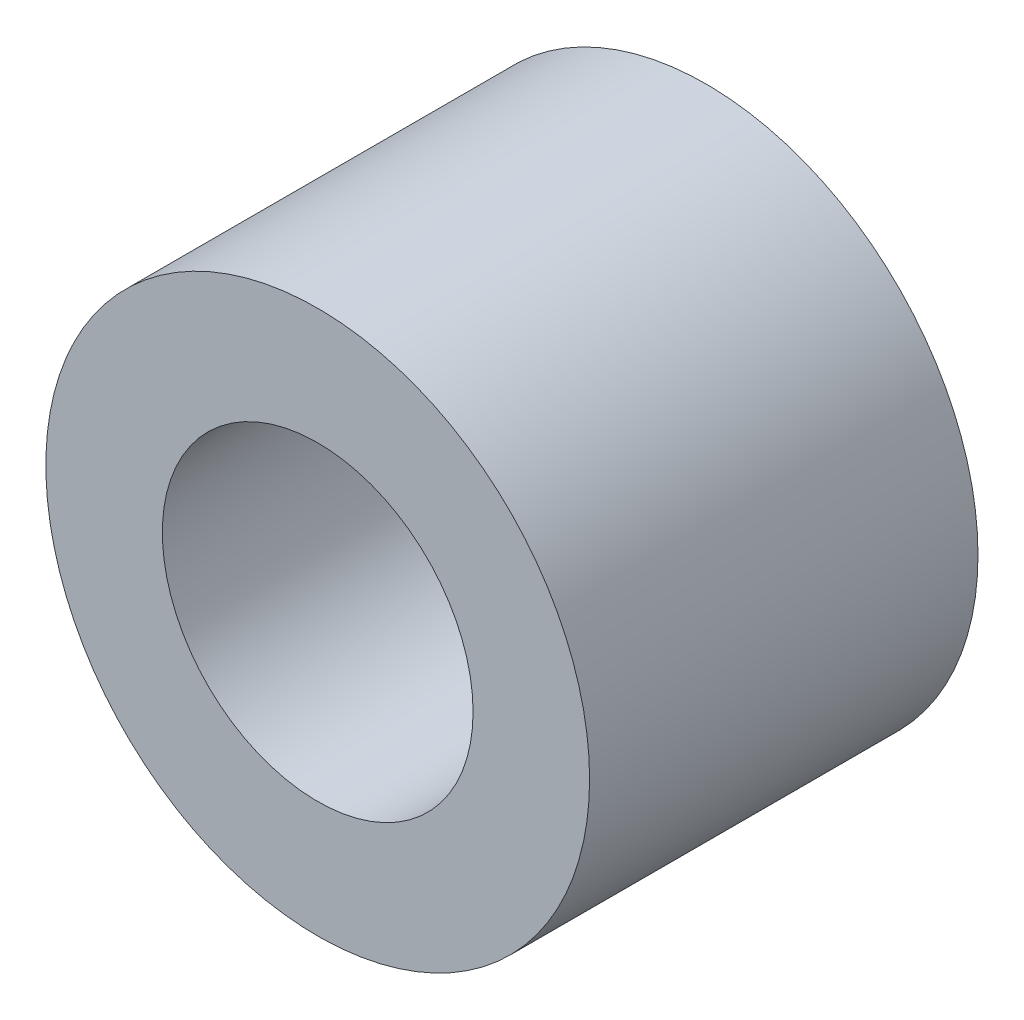
SolidWorks part; units mm, degrees
material "Alumina"
ref_plane "Plan de face" through (0, 0, 0) normal (0, 0, 1) x (1, 0, 0)
ref_plane "Plan de dessus" through (0, 0, 0) normal (0, 1, 0) x (1, 0, 0)
ref_plane "Plan de droite" through (0, 0, 0) normal (1, 0, 0) x (0, 0, -1)
sketch "Sketch1" plane through (0, 0, 0) normal (0, 0, 1) x (1, 0, 0)
  circle A0 centre (0, 0) radius 7
  circle A1 centre (0, 0) radius 4
  dimension "D1" = 8
  dimension "D2" = 14
extrude "Boss-Extrude1" add sketch "Sketch1" along normal blind 10
